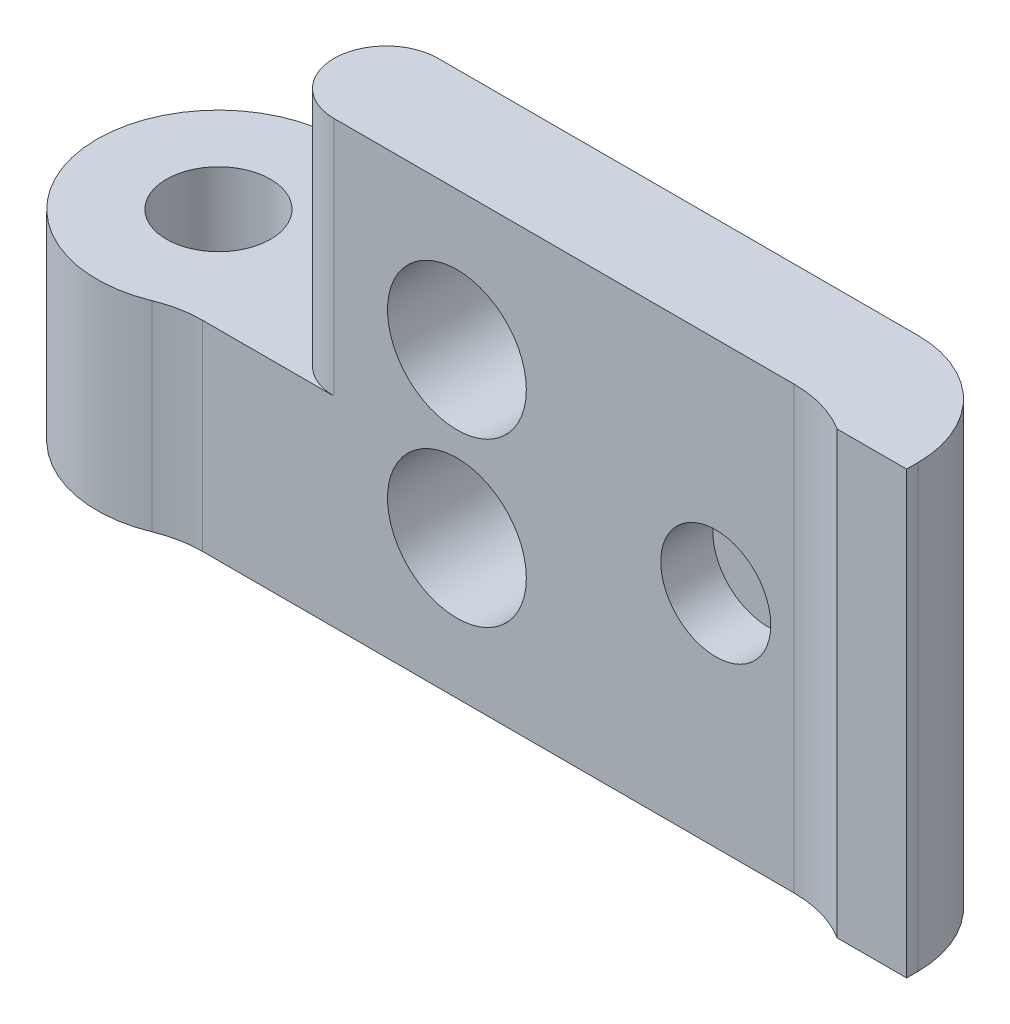
SolidWorks part; units mm, degrees
ref_plane "Front Plane" through (0, 0, 0) normal (0, 0, 1) x (1, 0, 0)
ref_plane "Top Plane" through (0, 0, 0) normal (0, 1, 0) x (1, 0, 0)
ref_plane "Right Plane" through (0, 0, 0) normal (1, 0, 0) x (0, 0, -1)
sketch "Sketch1" plane through (0, 0, 0) normal (0, 1, 0) x (1, 0, 0)
  line L0 (3.5, 0) -> (23.3302, 0)
  line L1 (23.3302, 0) -> (23.3302, 3)
  line L2 (23.3302, 3) -> (1.8028, 3)
  line L3 (23.3302, 4) -> (23.3302, 7) construction
  line L4 (0, 4) -> (23.3302, 4) construction
  circle A0 centre (0, 0) radius 3.5
  dimension "D1" = 7
  dimension "D2" = 3
  dimension "D3" = 1
extrude "Boss-Extrude1" add sketch "Sketch1" along normal blind 12.7
sketch "Sketch2" plane through (0, 12.7, 0) normal (0, 1, 0) x (1, 0, 0)
  line L0 (3.5, 0) -> (23.3302, 0) construction
  line L1 (23.3302, 3) -> (1.8028, 3) construction
  line L2 (6.3302, 0) -> (6.3302, 3) construction
  line L3 (23.3302, 0) -> (23.3302, 3) construction
  arc A0 (6.3302, 0) -> (6.3302, 3) centre (6.3302, 1.5) cw
  arc A1 (6.3302, 0) -> (6.3302, 3) centre (0.1803, 1.5) cw
  line M3 (23.3302, 3) -> (1.8028, 3)
  arc M4 (1.8028, 3) -> (3.5, 0) centre (0, 0) ccw
  line M5 (3.5, 0) -> (23.3302, 0)
  dimension "D1" = 17
extrude "Cut-Extrude1" cut sketch "Sketch2" against normal up to surface (6.93 mm away) contours A1 M5 M4 M3 | A0 M5 M3 M4
sketch "Sketch3" plane through (0, 5.77, 0) normal (0, 1, 0) x (1, 0, 0)
  circle A0 centre (0, 0) radius 1.5
  dimension "D1" = 3
extrude "Cut-Extrude2" cut sketch "Sketch3" against normal through all
ref_plane "Plane1" through (0, 0, -5) normal (0, 0, 1) x (1, 0, 0)
mirror "Mirror1" about plane through (0, 0, -5) normal (0, 0, 1) of bodies 103
delete or keep bodies "Body-Delete1" type delete bodies bodies 103
sketch "Sketch4" plane through (0, 0, -7) normal (0, 0, 1) x (1, 0, 0)
  circle A0 centre (9.8715, 8.7) radius 2
  circle A1 centre (9.8715, 4) radius 2
  dimension "D1" = 4
extrude "Cut-Extrude3" cut sketch "Sketch4" against normal blind 10
sketch "Sketch5" plane through (0, 12.7, 0) normal (0, 1, 0) x (1, 0, 0)
  line L0 (23.3302, 7) -> (6.3302, 7) construction
  line L1 (23.3302, 7) -> (21.3302, 7)
  line L2 (23.3302, 7) -> (23.3302, 6.5)
  line L3 (23.3302, 6.5) -> (21.3302, 6.5)
  line L4 (21.3302, 7) -> (21.3302, 6.5)
  arc A0 (21.3302, 6.5) -> (19.591, 7) centre (19.591, 3.725) ccw
  arc A1 (19.591, 2) -> (21.3302, 2.5) centre (19.591, 5.275) ccw construction
  line M2 (6.3302, 7) -> (23.3302, 7)
  dimension "D1" = 0.5
  dimension "D2" = 2
extrude "Boss-Extrude2" add sketch "Sketch5" against normal up to surface (12.7 mm away) contours A0 L4 M2 | L4 L3 L2 M2
fillet "Fillet1" radius 3.175 3 edges at (1.8028, 2.885, -7) (3.5, 2.885, -10) (23.3302, 6.35, -10)
sketch "Sketch6" plane through (0, 0, -7) normal (0, 0, 1) x (1, 0, 0)
  circle A0 centre (17.3302, 6.35) radius 1.585
  circle A1 centre (17.3302, 6.35) radius 1.585 construction
extrude "Cut-Extrude4" cut sketch "Sketch6" against normal blind 1.5
